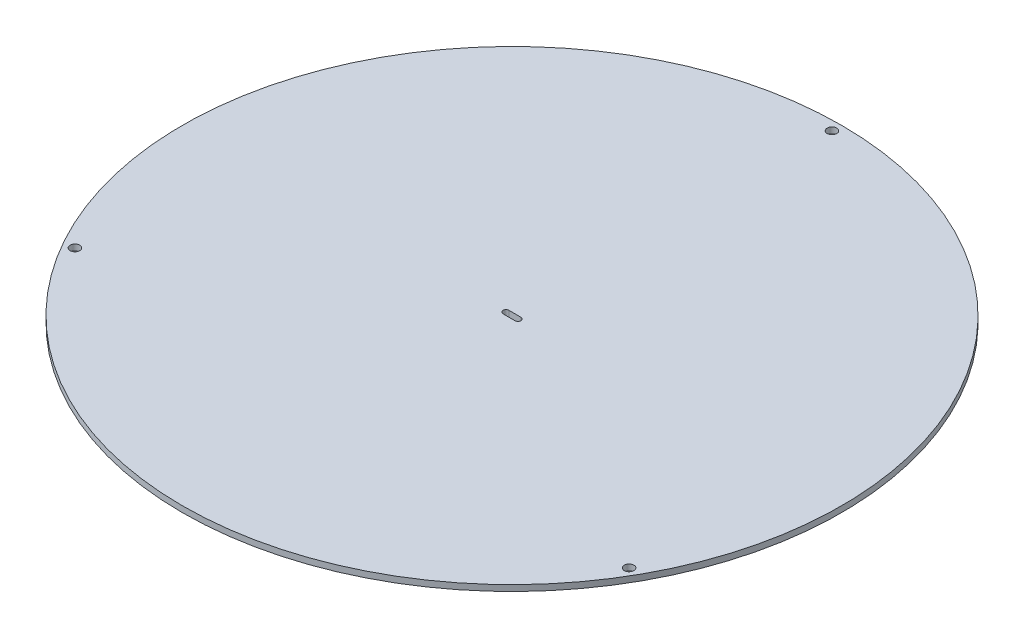
SolidWorks part; units mm, degrees
ref_plane "Plan de face" through (0, 0, 0) normal (0, 0, 1) x (1, 0, 0)
ref_plane "Plan de dessus" through (0, 0, 0) normal (0, 1, 0) x (1, 0, 0)
ref_plane "Plan de droite" through (0, 0, 0) normal (1, 0, 0) x (0, 0, -1)
sketch "Esquisse1" plane through (0, 0, 0) normal (0, 1, 0) x (1, 0, 0)
  line L0 (-2, 0) -> (2, 0) construction
  line L1 (-2, 1) -> (2, 1)
  line L2 (-2, -1) -> (2, -1)
  circle A0 centre (0, 0) radius 110
  arc A1 (-2, 1) -> (-2, -1) centre (-2, 0) ccw
  arc A2 (2, -1) -> (2, 1) centre (2, 0) ccw
  point P5 (0, 0)
  dimension "D1" = 220
  dimension "D2" = 4
  dimension "D3" = 1
extrude "Boss.-Extru.1" add sketch "Esquisse1" along normal blind 2
sketch "Esquisse2" plane through (0, 2, 0) normal (0, 1, 0) x (1, 0, 0)
  line L0 (0, 0) -> (0, 106.8) construction
  circle A0 centre (0, 0) radius 106.8 construction
  circle A1 centre (0, 106.8) radius 1.6
  dimension "D1" = 106.8
  dimension "D2" = 3.2
extrude "Enlèv. mat.-Extru.1" cut sketch "Esquisse2" against normal through all
pattern_circular "Répétition circulaire2" count 3 over 360 about axis through (0, 0, 0) along (0, 1, 0) of "Enlèv. mat.-Extru.1"
